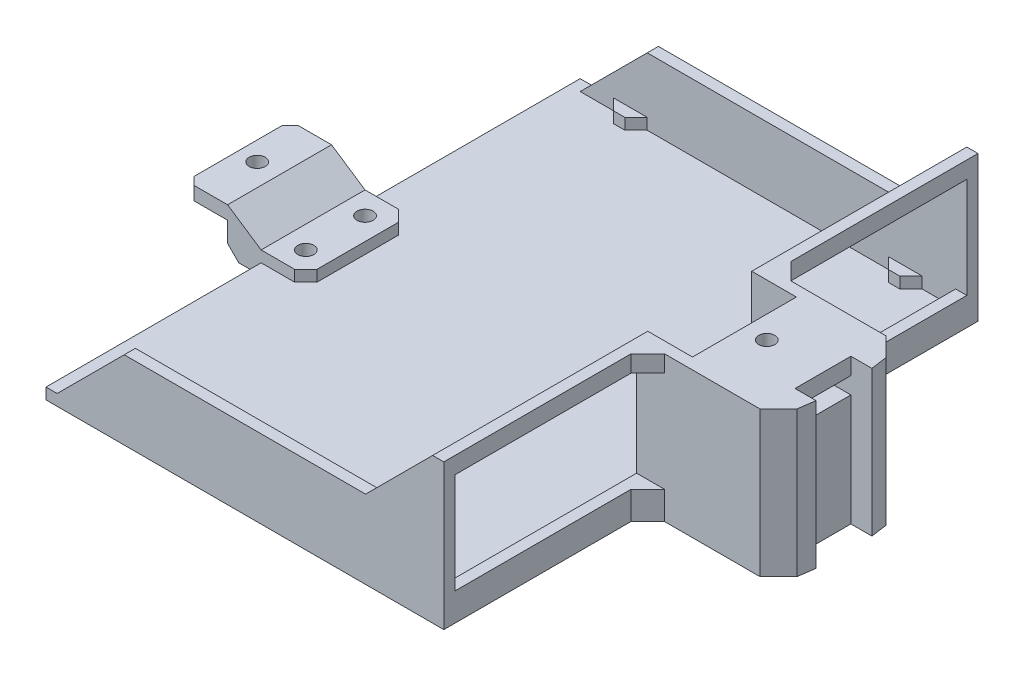
SolidWorks part; units mm, degrees
ref_plane "Front Plane" through (0, 0, 0) normal (0, 0, 1) x (1, 0, 0)
ref_plane "Top Plane" through (0, 0, 0) normal (0, 1, 0) x (1, 0, 0)
ref_plane "Right Plane" through (0, 0, 0) normal (1, 0, 0) x (0, 0, -1)
sketch "Sketch1" plane through (0, 0, 0) normal (0, 1, 0) x (1, 0, 0)
  line L0 (-1000, 0) -> (49000, 0) construction
  line L1 (6.35, -70.6772) -> (-6.35, -70.6772)
  line L2 (70.231, 6.35) -> (75.935, 6.35) construction
  line L3 (70.231, 6.35) -> (70.231, -6.35) construction
  line L4 (70.231, -6.35) -> (75.935, -6.35) construction
  line L5 (75.935, 6.35) -> (75.935, -6.35) construction
  line L6 (70.6772, 6.35) -> (75.4524, 6.35)
  line L7 (70.6772, 6.35) -> (70.6772, -6.35)
  line L8 (70.6772, -6.35) -> (75.4524, -6.35)
  line L9 (75.4524, 6.35) -> (75.4524, -6.35)
  line L10 (6.35, -70.6772) -> (6.35, -75.4524)
  line L11 (6.35, -75.4524) -> (-6.35, -75.4524)
  line L12 (-6.35, -70.6772) -> (-6.35, -75.4524)
  line L13 (-70.6772, -6.35) -> (-70.6772, 6.35)
  line L14 (-70.6772, -6.35) -> (-75.4524, -6.35)
  line L15 (-75.4524, -6.35) -> (-75.4524, 6.35)
  line L16 (-70.6772, 6.35) -> (-75.4524, 6.35)
  line L17 (-6.35, 70.6772) -> (6.35, 70.6772)
  line L18 (-6.35, 70.6772) -> (-6.35, 75.4524)
  line L19 (-6.35, 75.4524) -> (6.35, 75.4524)
  line L20 (6.35, 70.6772) -> (6.35, 75.4524)
  circle A0 centre (0, 0) radius 75.692 construction
  circle A1 centre (0, 0) radius 76.2 construction
  circle A2 centre (0, 0) radius 70.231 construction
  point P10 (75.935, 0)
  point P31 (0, 0)
  dimension "D1" = 151.384
  dimension "D2" = 152.4
  dimension "D5" = 140.462
  dimension "D3" = 12.7
  dimension "D4" = 0.4826
  dimension "D6" = 4.7752
  dimension "D7" = 4
sketch "Sketch3" plane through (0, 0, 0) normal (0, 1, 0) x (1, 0, 0)
  line L1 (-45.2113, -60.706) -> (45.2113, -60.706)
  line L2 (-45.2113, -60.706) -> (-45.2113, 60.706)
  line L3 (-45.2113, 60.706) -> (45.2113, 60.706)
  line L4 (45.2113, -60.706) -> (45.2113, 60.706)
  line L5 (-45.2113, -60.706) -> (45.2113, 60.706) construction
  line L6 (-45.2113, 60.706) -> (45.2113, -60.706) construction
  circle A0 centre (0, 0) radius 75.692 construction
  point P0 (0, 0)
  dimension "D1" = 121.412
extrude "Boss-Extrude4" add sketch "Sketch3" along normal blind 2.54
sketch "Sketch6" plane through (0, 2.54, 0) normal (0, 1, 0) x (1, 0, 0)
  line L0 (-1000, 0) -> (49000, 0) construction
  line L1 (45.2113, -60.706) -> (45.2113, 60.706) construction
  line L2 (45.2113, 60.706) -> (-45.2113, 60.706) construction
  line L3 (45.2113, -60.706) -> (45.2113, 60.706)
  line L4 (45.2113, 60.706) -> (-45.2113, 60.706)
  line L5 (-45.2113, 60.706) -> (-45.2113, 58.166)
  line L6 (-45.2113, 60.706) -> (-45.2113, -60.706) construction
  line L7 (-45.2113, 58.166) -> (42.6713, 58.166)
  line L8 (42.6713, 58.166) -> (42.6713, -58.166)
  line L10 (-45.2113, -58.166) -> (42.6713, -58.166)
  line L11 (-45.2113, -60.706) -> (-45.2113, -58.166)
  line L12 (45.2113, -60.706) -> (-45.2113, -60.706)
  dimension "D1" = 2.54
  dimension "D2" = 2.54
extrude "Boss-Extrude5" add sketch "Sketch6" along normal blind 30.48
sketch "Sketch7" plane through (0, 0, 60.706) normal (0, 0, 1) x (1, 0, 0)
  line L0 (42.6713, 2.54) -> (-45.2113, 2.54) construction
  line L1 (42.6713, 33.02) -> (42.6713, 2.54) construction
  line L2 (42.6713, 2.54) -> (-45.2113, 2.54) construction
  line L3 (42.6713, 33.02) -> (42.6713, 2.54) construction
  line L4 (0, -1000) -> (0, 49000) construction
  line L5 (-957.3287, 17.78) -> (49042.6713, 17.78) construction
  line L6 (-42.6713, 33.02) -> (-42.6713, 2.54) construction
  line L7 (-42.6713, 2.54) -> (-27.4313, 17.78)
  line L8 (-27.4313, 17.78) -> (27.4313, 17.78)
  line L9 (27.4313, 17.78) -> (42.6713, 33.02)
  line L10 (42.6713, 33.02) -> (-45.2113, 33.02)
  line L11 (-45.2113, 33.02) -> (-45.2113, 2.54)
  line L12 (-45.2113, 2.54) -> (-42.6713, 2.54)
  point P9 (42.6713, 17.78)
  dimension "D1" = 45
  dimension "D2" = 45
extrude "Cut-Extrude2" cut sketch "Sketch7" against normal through all
sketch "Sketch8" plane through (0, 0, 0) normal (0, 1, 0) x (1, 0, 0)
  line L0 (-1000, 0) -> (49000, 0) construction
  line L1 (45.2113, 14.351) -> (70.694, 14.351)
  line L2 (45.2113, -60.706) -> (45.2113, 60.706) construction
  line L3 (70.694, 14.351) -> (74.9221, 10.1229)
  line L4 (74.9221, 10.1229) -> (75.4524, 6.35)
  line L5 (75.4524, 6.35) -> (70.6772, 6.35)
  line L6 (70.6772, 6.35) -> (70.6772, -6.35)
  line L7 (45.2113, 14.351) -> (45.2113, -14.351)
  line L8 (45.2113, -14.351) -> (70.694, -14.351)
  line L9 (70.694, -14.351) -> (74.9221, -10.1229)
  line L10 (74.9221, -10.1229) -> (75.4524, -6.35)
  line L11 (75.4524, -6.35) -> (70.6772, -6.35)
  line L13 (70.6772, 6.35) -> (70.6772, -6.35) construction
  line L14 (70.6772, 6.35) -> (75.4524, 6.35) construction
  point P13 (45.2113, 0)
  point P17 (70.6772, 0)
  dimension "D1" = 82
  dimension "D2" = 135
  dimension "D3" = 28.702
  dimension "D4" = 3.81
extrude "Boss-Extrude6" add sketch "Sketch8" along normal up to surface (33.02 mm away) up to face at (43.518, 33.02, 0)
sketch "Sketch9" plane through (0, 33.02, 0) normal (0, 1, 0) x (1, 0, 0)
  line L0 (-1000, 0) -> (49000, 0) construction
  line L1 (52.8313, -11.811) -> (52.8313, 11.811)
  line L2 (52.8313, 11.811) -> (42.6713, 11.811)
  line L3 (42.6713, 58.166) -> (42.6713, -58.166) construction
  line L4 (42.6713, 11.811) -> (42.6713, -11.811)
  line L5 (52.8313, -11.811) -> (42.6713, -11.811)
  line L6 (70.694, 14.351) -> (45.2113, 14.351) construction
  point P10 (42.6713, 0)
  point P11 (52.8313, 0)
  dimension "D1" = 10.16
  dimension "D2" = 2.54
extrude "Cut-Extrude3" cut sketch "Sketch9" against normal offset from surface (27.94 mm away) 2.54 up to face at (-21.9706, 2.54, 0)
sketch "Sketch11" plane through (0, 2.54, 0) normal (0, 1, 0) x (1, 0, 0)
  line L5 (35.0513, 58.166) -> (27.4313, 58.166)
  line L6 (-42.6713, 58.166) -> (42.6713, 58.166) construction
  line L7 (27.4313, 58.166) -> (29.9713, 55.626)
  line L8 (29.9713, 55.626) -> (32.5113, 55.626)
  line L9 (32.5113, 55.626) -> (35.0513, 58.166)
  line L10 (42.6713, 58.166) -> (42.6713, -58.166) construction
  line L11 (-1000, 0) -> (49000, 0) construction
  line L12 (0, -1000) -> (0, 49000) construction
  line L13 (-29.9713, 55.626) -> (-32.5113, 55.626)
  line L14 (-27.4313, 58.166) -> (-29.9713, 55.626)
  line L15 (-35.0513, 58.166) -> (-27.4313, 58.166)
  line L16 (-32.5113, 55.626) -> (-35.0513, 58.166)
  line L17 (29.9713, -55.626) -> (32.5113, -55.626)
  line L18 (27.4313, -58.166) -> (29.9713, -55.626)
  line L19 (35.0513, -58.166) -> (27.4313, -58.166)
  line L20 (32.5113, -55.626) -> (35.0513, -58.166)
  line L21 (-27.4313, -58.166) -> (-29.9713, -55.626)
  line L22 (-35.0513, -58.166) -> (-27.4313, -58.166)
  line L23 (-32.5113, -55.626) -> (-35.0513, -58.166)
  line L24 (-29.9713, -55.626) -> (-32.5113, -55.626)
  dimension "D1" = 45
  dimension "D2" = 45
  dimension "D3" = 2.54
  dimension "D4" = 2.54
  dimension "D5" = 7.62
extrude "Boss-Extrude7" add sketch "Sketch11" along normal up to surface (2.54 mm away) up to face at (47.7513, 5.08, 0)
sketch "Sketch12" plane through (52.8313, 0, 0) normal (-1, 0, 0) x (0, 0, 1)
  line L0 (11.811, 5.08) -> (11.811, 33.02) construction
  line L1 (11.811, 29.21) -> (-11.811, 29.21)
  line L2 (11.811, 29.21) -> (11.811, 25.4)
  line L3 (11.811, 25.4) -> (-11.811, 25.4)
  line L4 (-11.811, 29.21) -> (-11.811, 25.4)
  line L5 (-11.811, 5.08) -> (-11.811, 33.02) construction
  line L6 (11.811, 33.02) -> (-11.811, 33.02) construction
  dimension "D1" = 3.81
  dimension "D2" = 3.81
extrude "Cut-Extrude4" cut sketch "Sketch12" against normal blind 10.16
sketch "Sketch13" plane through (62.9913, 0, 0) normal (-1, 0, 0) x (0, 0, 1)
  line L0 (11.811, 29.21) -> (-11.811, 29.21) construction
  line L1 (-6.35, 29.21) -> (6.35, 29.21)
  line L2 (-6.35, 29.21) -> (-6.35, 25.4)
  line L3 (-6.35, 25.4) -> (6.35, 25.4)
  line L4 (6.35, 29.21) -> (6.35, 25.4)
  line L5 (-6.35, 33.02) -> (-6.35, 0) construction
  line L6 (-11.811, 25.4) -> (11.811, 25.4) construction
  line L7 (6.35, 33.02) -> (6.35, 0) construction
extrude "Cut-Extrude5" cut sketch "Sketch13" against normal through all
sketch "Sketch15" plane through (0, 0, 0) normal (0, 0, 1) x (1, 0, 0)
  line L0 (0, -1000) -> (0, 49000) construction
  line L2 (62.9913, 29.21) -> (62.9913, 25.4) construction
  line L3 (62.9913, 25.4) -> (52.8313, 25.4) construction
  line L4 (62.9913, 29.21) -> (52.8313, 29.21) construction
  line L5 (62.9913, 25.4) -> (52.8313, 25.4) construction
  line L6 (62.9913, 29.21) -> (62.9913, 25.4) construction
  line L7 (62.9913, 29.21) -> (52.8313, 29.21) construction
  line L8 (-62.9913, 29.21) -> (-52.8313, 29.21) construction
  line L9 (-62.9913, 29.21) -> (-62.9913, 25.4) construction
  line L10 (-62.9913, 25.4) -> (-52.8313, 25.4) construction
  line L11 (-998.1426, 17.78) -> (49001.8574, 17.78) construction
  line L13 (-62.9913, 10.16) -> (-52.8313, 10.16)
  line L14 (-62.9913, 6.35) -> (-62.9913, 10.16)
  line L15 (-62.9913, 6.35) -> (-52.8313, 6.35)
  line L16 (-27.4313, 17.78) -> (27.4313, 17.78) construction
  line L17 (-52.8313, 6.35) -> (-52.8313, 0)
  line L18 (-52.8313, 0) -> (-45.2113, 0)
  line L19 (-45.2113, 0) -> (-45.2113, 2.54)
  line L20 (-45.2113, 2.54) -> (-35.0513, 2.54)
  line L21 (-35.0513, 2.54) -> (-42.6713, 2.54) construction
  line L23 (-35.0513, 2.54) -> (-35.0513, 5.08)
  line L24 (-35.0513, 5.08) -> (-45.2113, 5.08)
  line L25 (-45.2113, 5.08) -> (-52.8313, 10.16)
  line L26 (-27.4313, 5.08) -> (-35.0513, 5.08) construction
  line L27 (52.8313, 5.08) -> (42.6713, 5.08) construction
  line L28 (52.8313, 5.08) -> (42.6713, 5.08) construction
extrude "Boss-Extrude9" add sketch "Sketch15" against normal up to surface and the other way up to surface up to face at (52.8313, 23.1775, -11.811) other way up to face at (52.8313, 23.1775, 11.811)
hole_wizard "CBORE for #6 Pan Head Machine Screw1" positions "Sketch16" profile "Sketch17" counterbore size "#6" standard "ANSI Inch" end condition through all
sketch "Sketch16" plane through (0, 0, 0) normal (0, -1, 0) x (-1, 0, 0)
  line L0 (-47.7513, -988.189) -> (-47.7513, 49011.811) construction
  line L1 (-52.8313, 11.811) -> (-42.6713, 11.811) construction
  line L2 (-1000, 0) -> (49000, 0) construction
  line L3 (40.1313, -988.189) -> (40.1313, 49011.811) construction
  line L4 (45.2113, 11.811) -> (35.0513, 11.811) construction
  line L5 (-1047.7513, 6.731) -> (48952.2487, 6.731) construction
  line L6 (-1047.7513, -6.731) -> (48952.2487, -6.731) construction
  line L7 (-52.8313, 11.811) -> (-42.6713, 1.651) construction
  line L8 (-42.6713, 11.811) -> (-42.6713, -11.811) construction
  point P0 (-47.7513, 6.731)
  point P7 (-47.7513, 11.811)
  point P18 (-47.7513, -6.731)
  point P24 (40.1313, 11.811)
  point P34 (40.1313, 6.731)
  point P36 (40.1313, -6.731)
  dimension "D1" = 45
sketch "Sketch17" plane through (47.7513, 0, -6.731) normal (1, 0, 0) x (0, 0, -1)
  line L0 (0, 0) -> (0, 33.02)
  line L1 (0, 33.02) -> (1.8288, 33.02)
  line L3 (1.8288, 33.02) -> (1.8288, 2.4638)
  line L4 (1.8288, 2.4638) -> (3.7706, 2.4638)
  line L5 (3.7706, 2.4638) -> (3.7706, 0)
  line L7 (3.7706, 0) -> (0, 0)
  line L11 (0, -6.35) -> (0, 107.95) construction
  dimension "Thru Hole Dia." = 3.6576
  dimension "Thru Hole Depth" = 33.02
  dimension "C'Bore Dia." = 7.5413
  dimension "C'Bore Depth" = 2.4638
hole_wizard "#6 Clearance Hole1" positions "Sketch19" profile "Sketch20" hole size "#6" standard "ANSI Inch" end condition through all
sketch "Sketch19" plane through (0, 33.02, 0) normal (0, 1, 0) x (1, 0, 0)
  line L0 (-1000, 0) -> (49000, 0) construction
  line L1 (0, -1000) -> (0, 49000) construction
  line L2 (57.9113, -988.189) -> (57.9113, 49011.811) construction
  line L3 (62.9913, 11.811) -> (52.8313, 11.811) construction
  point P6 (57.9113, 0)
  point P13 (-57.9113, 0)
  point P20 (57.9113, 11.811)
sketch "Sketch20" plane through (-57.9113, 33.02, 0) normal (1, 0, 0) x (0, 0, 1)
  line L0 (0, 0) -> (0, 33.02)
  line L1 (0, 33.02) -> (1.8288, 33.02)
  line L2 (1.8288, 33.02) -> (1.8288, 0)
  line L5 (1.8288, 0) -> (0, 0)
  line L11 (0, -6.35) -> (0, 107.95) construction
  dimension "Thru Hole Dia." = 3.6576
  dimension "Thru Hole Depth" = 33.02
sketch "Sketch21" plane through (42.6713, 0, 0) normal (-1, 0, 0) x (0, 0, 1)
  line L0 (-1058.166, 17.78) -> (48941.834, 17.78) construction
  line L1 (-58.166, 33.02) -> (-58.166, 2.54) construction
  line L2 (0, -1000) -> (0, 49000) construction
  line L3 (-11.811, 0) -> (11.811, 0) construction
  line L9 (-1008.4655, 5.08) -> (48991.5345, 5.08) construction
  line L10 (-58.166, 6.35) -> (-58.166, 29.21)
  line L11 (-11.811, 5.08) -> (11.811, 5.08) construction
  line L14 (-58.166, 29.21) -> (-14.351, 29.21)
  line L15 (-14.351, 29.21) -> (-14.351, 6.35)
  line L18 (-58.166, 6.35) -> (-14.351, 6.35)
  line L20 (58.166, 29.21) -> (14.351, 29.21)
  line L21 (58.166, 6.35) -> (58.166, 29.21)
  line L22 (58.166, 6.35) -> (14.351, 6.35)
  line L23 (14.351, 29.21) -> (14.351, 6.35)
  line L24 (-58.166, 33.02) -> (-58.166, 17.78) construction
  line L25 (-14.351, 33.02) -> (-14.351, 0) construction
  point P5 (-58.166, 17.78)
  point P10 (0, 0)
  point P19 (-14.351, 17.78)
  point P20 (-58.166, 17.78)
  dimension "D1" = 1.27
extrude "Cut-Extrude6" cut sketch "Sketch21" against normal through all
chamfer "Chamfer1" distance 2.54 angle 45 5 edges at (-62.9913, 8.255, -11.811) (-62.9913, 8.255, 11.811) (-35.0513, 3.81, 11.811) (-35.0513, 3.81, -11.811) (-52.8313, 0, 0)
chamfer "Chamfer2" distance 3.81 angle 45 4 edges at (45.2113, 3.175, -14.351) (45.2113, 3.175, 14.351) (45.2113, 31.115, -14.351) (45.2113, 31.115, 14.351)
sketch "Sketch23" plane through (0, 6.35, 0) normal (0, -1, 0) x (1, 0, 0)
  line L0 (-62.9913, -9.271) -> (-62.9913, 9.271) construction
  line L1 (-52.8313, 11.811) -> (-62.9913, 11.811)
  line L2 (-52.8313, 11.811) -> (-52.8313, -11.811)
  line L3 (-52.8313, -11.811) -> (-62.9913, -11.811)
  line L4 (-62.9913, 11.811) -> (-62.9913, -11.811)
  line L5 (-60.4513, -11.811) -> (-52.8313, -11.811) construction
extrude "Cut-Extrude8" cut sketch "Sketch23" against normal blind 0.762
chamfer "Chamfer3" distance 0.762 angle 45 2 edges at (-62.9913, 7.112, 0) (-62.9913, 10.16, 0)
